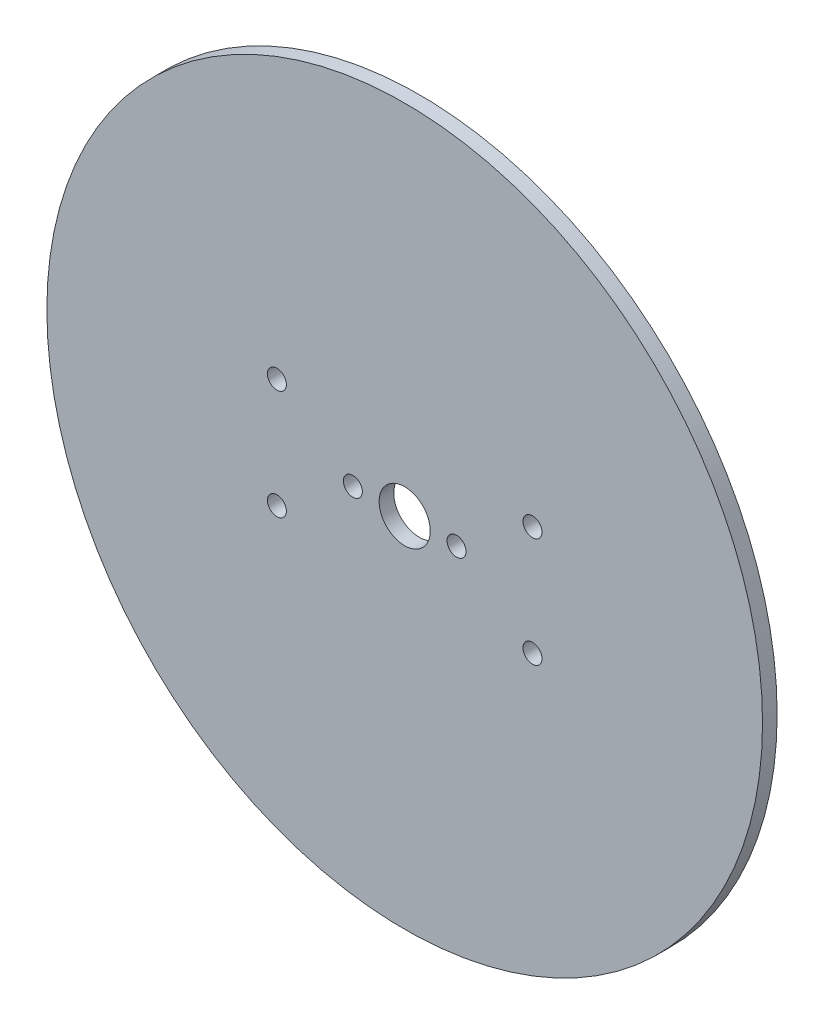
SolidWorks part; units mm, degrees
ref_plane "Blat stołu" through (0, 0, 0) normal (0, 0, 1) x (1, 0, 0)
ref_plane "Płaszczyzna górna" through (0, 0, 0) normal (0, 1, 0) x (1, 0, 0)
ref_plane "Płaszczyzna prawa" through (0, 0, 0) normal (1, 0, 0) x (0, 0, -1)
sketch "Szkic1" plane through (0, 0, 0) normal (0, 0, 1) x (1, 0, 0)
  circle A0 centre (0, 0) radius 49
  dimension "D1" = 98
extrude "Dodanie-wyciągnięcie1" add sketch "Szkic1" along normal blind 2
sketch "Szkic2" plane through (0, 0, 0) normal (0, 0, -1) x (-1, 0, 0)
  point P0 (7.1, 0)
  point P1 (-7.1, 0)
  dimension "7,1" = 7.1
  dimension "D2" = 14.2
sketch "Szkic4" plane through (0, 0, 0) normal (0, 0, -1) x (-1, 0, 0)
  circle A0 centre (0, 0) radius 3.5
  dimension "D1" = 7
extrude "Wytnij-wyciągnięcie2" cut sketch "Szkic4" against normal up to next
sketch "Szkic5" plane through (0, 0, 0) normal (0, 0, -1) x (-1, 0, 0)
  point P0 (17.5, 7.5)
  point P1 (17.5, -7.5)
  point P2 (-17.5, -7.5)
  point P3 (-17.5, 7.5)
  dimension "D1" = 35
  dimension "D2" = 15
  dimension "D3" = 7.5
  dimension "D4" = 17.5
hole_wizard "Otwór pod śrubę M21" positions "Szkic 3D1" profile "Szkic6" hole size "M2" standard "ISO" end condition up to next
sketch3d "Szkic 3D1"
  point P0 (-17.5, 7.5, 0)
  point P3 (-17.5, -7.5, 0)
  point P6 (17.5, -7.5, 0)
  point P9 (17.5, 7.5, 0)
sketch "Szkic6" plane through (-17.5, 7.5, 0) normal (1, 0, 0) x (0, 1, 0)
  line L0 (0, 0) -> (0, 2)
  line L1 (0, 2) -> (1.3, 2)
  line L2 (1.3, 2) -> (1.3, 0)
  line L5 (1.3, 0) -> (0, 0)
  line L11 (0, -6.35) -> (0, 107.95) construction
  dimension "Średnica otworu na wylot" = 2.6
  dimension "Głębokość otworu na wylot" = 2
hole_wizard "Otwór pod śrubę M22" positions "Szkic 3D2" profile "Szkic7" hole size "M2" standard "ISO" end condition up to next
sketch3d "Szkic 3D2"
  point P0 (-7.1, 0, 0)
  point P3 (7.1, 0, 0)
sketch "Szkic7" plane through (-7.1, 0, 0) normal (1, 0, 0) x (0, 1, 0)
  line L0 (0, 0) -> (0, 2)
  line L1 (0, 2) -> (1.3, 2)
  line L2 (1.3, 2) -> (1.3, 0)
  line L5 (1.3, 0) -> (0, 0)
  line L11 (0, -6.35) -> (0, 107.95) construction
  dimension "Średnica otworu na wylot" = 2.6
  dimension "Głębokość otworu na wylot" = 2
